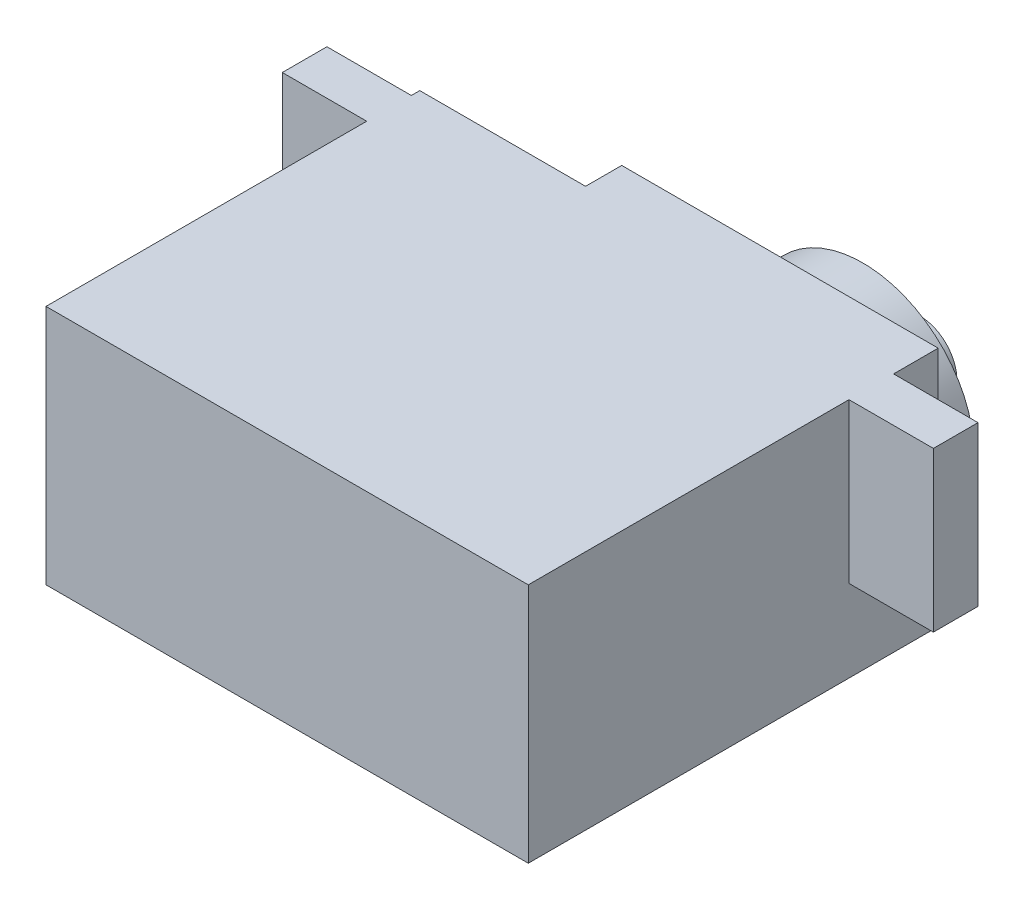
SolidWorks part; units mm, degrees
ref_plane "Front Plane" through (0, 0, 0) normal (0, 0, 1) x (1, 0, 0)
ref_plane "Top Plane" through (0, 0, 0) normal (0, 1, 0) x (1, 0, 0)
ref_plane "Right Plane" through (0, 0, 0) normal (1, 0, 0) x (0, 0, -1)
sketch "Sketch1" plane through (0, 0, 0) normal (0, 1, 0) x (1, 0, 0)
  line L1 (-20.9602, 14.8925) -> (19.0398, 14.8925)
  line L2 (-20.9602, 14.8925) -> (-20.9602, -19.1075)
  line L3 (-20.9602, -19.1075) -> (19.0398, -19.1075)
  line L4 (19.0398, 14.8925) -> (19.0398, -19.1075)
  dimension "D1" = 34
  dimension "D2" = 40
extrude "Boss-Extrude1" add sketch "Sketch1" along normal blind 20
sketch "Sketch2" plane through (0, 20, 0) normal (0, 1, 0) x (1, 0, 0)
  line L1 (-20.9602, 14.8925) -> (-7.2102, 14.8925)
  line L2 (-20.9602, 14.8925) -> (-20.9602, 11.8925)
  line L3 (-20.9602, 11.8925) -> (-7.2102, 11.8925)
  line L4 (-7.2102, 14.8925) -> (-7.2102, 11.8925)
  dimension "D1" = 3
  dimension "D2" = 13.75
extrude "Cut-Extrude1" cut sketch "Sketch2" against normal through all
sketch "Sketch3" plane through (0, 0, -14.8925) normal (0, 0, -1) x (-1, 0, 0)
  line L0 (-9.0398, 20) -> (20.9602, 20) construction
  line L1 (-9.0398, 20) -> (-9.0398, 0) construction
  line L3 (-19.0398, 0) -> (7.2102, 0) construction
  circle A0 centre (-9.0398, 10) radius 9.25
  circle A1 centre (-9.0398, 10) radius 3.05
  dimension "D1" = 18.5
  dimension "D2" = 6.1
extrude "Boss-Extrude2" add sketch "Sketch3" along normal blind 3.75 contours A1 | A0
sketch "Sketch4" plane through (0, 20, 0) normal (0, 1, 0) x (1, 0, 0)
  line L0 (19.0398, -19.1075) -> (19.0398, 7.4925)
  line L1 (19.0398, -19.1075) -> (19.0398, 14.8925) construction
  line L2 (19.0398, 7.4925) -> (-20.9602, 7.4925)
  line L3 (19.0398, 7.4925) -> (26.0398, 7.4925)
  line L4 (19.0398, 7.4925) -> (19.0398, 11.1925)
  line L5 (19.0398, 11.1925) -> (26.0398, 11.1925)
  line L6 (26.0398, 7.4925) -> (26.0398, 11.1925)
  line L7 (-20.9602, 11.8925) -> (-20.9602, -19.1075) construction
  line L9 (-20.9602, 7.4925) -> (-27.9602, 7.4925)
  line L10 (-20.9602, 7.4925) -> (-20.9602, 11.1925)
  line L11 (-20.9602, 11.1925) -> (-27.9602, 11.1925)
  line L12 (-27.9602, 7.4925) -> (-27.9602, 11.1925)
  line M3 (-20.9602, 11.8925) -> (-20.9602, -19.1075)
  line M5 (19.0398, -19.1075) -> (19.0398, 14.8925)
  dimension "D1" = 26.6
  dimension "D2" = 3.7
  dimension "D3" = 7
  dimension "D4" = 7
  dimension "D5" = 3.7
extrude "Boss-Extrude3" add sketch "Sketch4" against normal blind 13.2 contours L12 L9 L11 M3 | L3 L6 L5 M5
sketch "Sketch8" plane through (0, 0, -14.8925) normal (0, 0, -1) x (-1, 0, 0)
  circle A0 centre (-9.0398, 10) radius 3.05
extrude "Boss-Extrude5" add sketch "Sketch8" along normal blind 8.5
